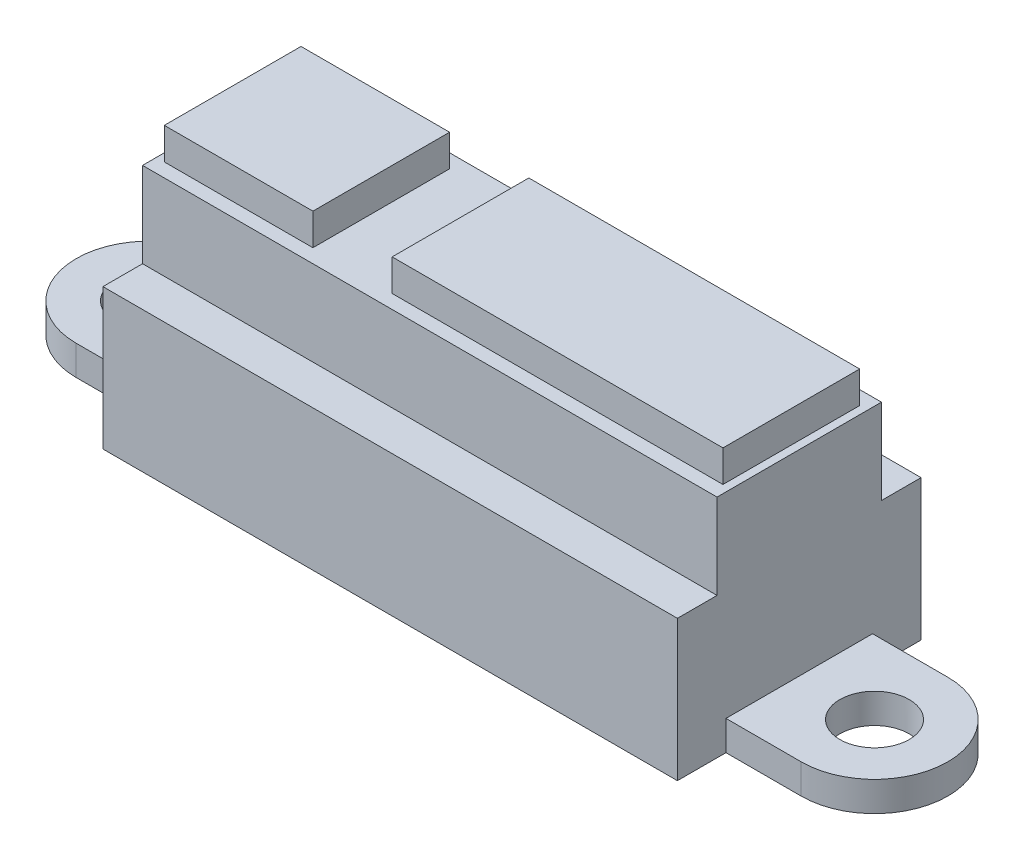
SolidWorks part; units mm, degrees
material "ABS"
ref_plane "Plano frontal" through (0, 0, 0) normal (0, 0, 1) x (1, 0, 0)
ref_plane "Plano superior" through (0, 0, 0) normal (0, 1, 0) x (1, 0, 0)
ref_plane "Plano direito" through (0, 0, 0) normal (1, 0, 0) x (0, 0, -1)
sketch "Esboço1" plane through (0, 0, 0) normal (0, 0, 1) x (1, 0, 0)
  line L0 (-14.1, 13) -> (-14.1, 11.4)
  line L1 (-14.1, 13) -> (-6.6, 13)
  line L2 (-14.5, 11.4) -> (-14.5, 1.5)
  line L3 (-14.5, 0) -> (14.5, 0)
  line L4 (-14.5, 1.5) -> (-22, 1.5)
  line L5 (-22, 1.5) -> (-22, 0)
  line L6 (-22, 0) -> (-14.5, 0)
  line L7 (-14.1, 11.4) -> (-14.5, 11.4)
  line L8 (14.1, 11.4) -> (14.5, 11.4)
  line L9 (22, 0) -> (14.5, 0)
  line L10 (0, 16.8208) -> (0, 0) construction
  line L11 (22, 1.5) -> (22, 0)
  line L12 (14.5, 1.5) -> (22, 1.5)
  line L13 (14.5, 11.4) -> (14.5, 1.5)
  line L14 (14.1, 13) -> (14.1, 11.4)
  line L15 (-6.6, 13) -> (-6.6, 11.4)
  line L16 (-6.6, 11.4) -> (-2.6, 11.4)
  line L17 (-2.6, 11.4) -> (-2.6, 13)
  line L18 (-2.6, 13) -> (14.1, 13)
  point P0 (0, 0)
  dimension "D1" = 29
  dimension "D2" = 13
  dimension "D3" = 1.6
  dimension "D4" = 0.4
  dimension "D5" = 44
  dimension "D6" = 1.5
  dimension "D7" = 7.5
  dimension "D8" = 4
extrude "Ressalto-extrusão1" add sketch "Esboço1" along normal blind 12.3
sketch "Esboço2" plane through (0, 13, 0) normal (0, 1, 0) x (1, 0, 0)
  line L0 (-22, -6.15) -> (22, -6.15) construction
  line L1 (-22, -12.3) -> (-22, 0) construction
  line L3 (-18.3, -2.45) -> (-14.5, -2.45)
  line L4 (-14.5, -12.3) -> (-14.5, 0) construction
  line L5 (-14.5, -2.45) -> (-14.5, 0)
  line L6 (-18.3, -9.85) -> (-14.5, -9.85)
  line L7 (-14.5, -9.85) -> (-14.5, -12.3)
  line L8 (-14.5, 0) -> (-22, 0)
  line L9 (-22, -12.3) -> (-22, 0)
  line L10 (-22, -12.3) -> (-14.5, -12.3)
  line L11 (0, 0) -> (0, -12.9333) construction
  line L12 (22, -12.3) -> (14.5, -12.3)
  line L13 (22, -12.3) -> (22, 0)
  line L14 (14.5, 0) -> (22, 0)
  line L15 (14.5, -9.85) -> (14.5, -12.3)
  line L16 (18.3, -9.85) -> (14.5, -9.85)
  line L17 (14.5, -2.45) -> (14.5, 0)
  line L18 (18.3, -2.45) -> (14.5, -2.45)
  arc A0 (-18.3, -2.45) -> (-18.3, -9.85) centre (-18.3, -6.15) ccw
  arc A1 (18.3, -2.45) -> (18.3, -9.85) centre (18.3, -6.15) cw
  circle A2 centre (-18.3, -6.15) radius 1.75
  circle A3 centre (18.3, -6.15) radius 1.75
  dimension "D1" = 7.4
  dimension "D2" = 3.5
  dimension "D3" = 36.6
extrude "Corte-extrusão1" cut sketch "Esboço2" against normal blind 22.3 contours A0 L9 L10 L7 L6 | A0 L3 L5 L8 L9 | L18 A1 L13 L14 L17 | L13 A1 L16 L15 L12 | A2 | A3
sketch "Esboço3" plane through (-14.5, 0, 0) normal (-1, 0, 0) x (0, 0, 1)
  line L0 (2.7, 13) -> (2.7, 11.4)
  line L1 (12.3, 13) -> (0, 13) construction
  line L2 (12.3, 11.4) -> (0, 11.4) construction
  line L3 (2.7, 11.4) -> (2, 11.4)
  line L4 (12.3, 11.4) -> (0, 11.4) construction
  line L5 (2, 11.4) -> (2, 7.1)
  line L6 (2, 7.1) -> (0, 7.1)
  line L7 (0, 11.4) -> (0, 0) construction
  line L8 (6.15, 13) -> (6.15, 6.194) construction
  line L9 (2.7, 13) -> (0, 13)
  line L10 (0, 13) -> (0, 7.1)
  line L11 (12.3, 13) -> (12.3, 7.1)
  line L12 (9.6, 13) -> (12.3, 13)
  line L13 (10.3, 7.1) -> (12.3, 7.1)
  line L14 (10.3, 11.4) -> (10.3, 7.1)
  line L15 (9.6, 11.4) -> (10.3, 11.4)
  line L16 (9.6, 13) -> (9.6, 11.4)
  dimension "D1" = 4.3
  dimension "D2" = 2
  dimension "D3" = 0.7
extrude "Corte-extrusão2" cut sketch "Esboço3" against normal blind 32.3
